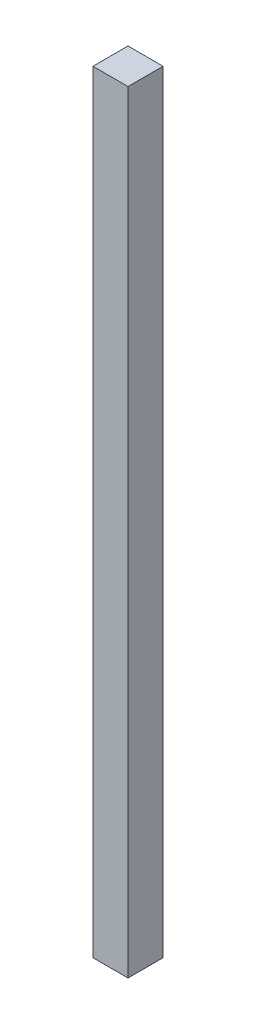
SolidWorks part; units mm, degrees
ref_plane "Front Plane" through (0, 0, 0) normal (0, 0, 1) x (1, 0, 0)
ref_plane "Top Plane" through (0, 0, 0) normal (0, 1, 0) x (1, 0, 0)
ref_plane "Right Plane" through (0, 0, 0) normal (1, 0, 0) x (0, 0, -1)
sketch "Sketch1" plane through (0, 0, 0) normal (0, 1, 0) x (1, 0, 0)
  line L1 (50, -50) -> (-50, -50)
  line L2 (50, -50) -> (50, 50)
  line L3 (50, 50) -> (-50, 50)
  line L4 (-50, -50) -> (-50, 50)
  line L5 (50, -50) -> (-50, 50) construction
  line L6 (50, 50) -> (-50, -50) construction
  point P0 (0, 0)
  dimension "D1" = 100
  dimension "D2" = 100
extrude "Boss-Extrude1" add sketch "Sketch1" along normal blind 2200
